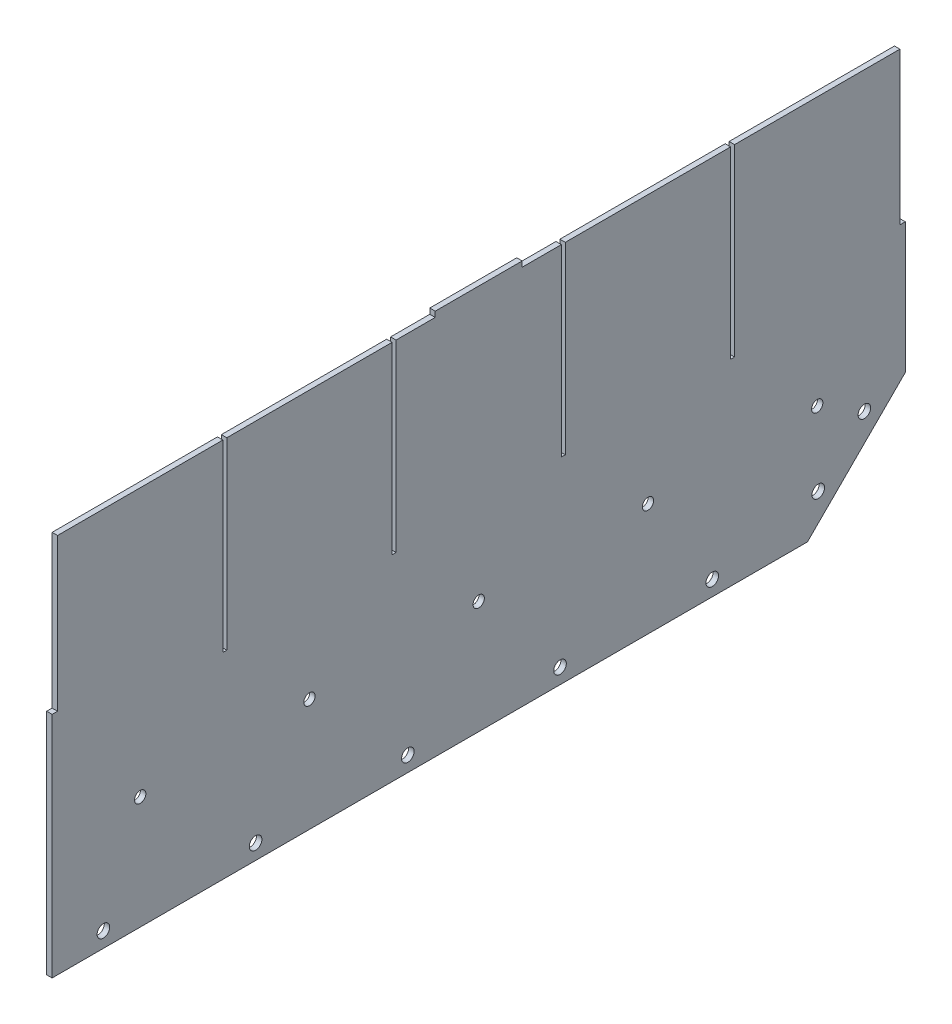
SolidWorks part; units mm, degrees
material "6061-T6 (SS)"
ref_plane "X-Y Datum" through (0, 0, 0) normal (0, 0, 1) x (1, 0, 0)
ref_plane "X-Z Datum" through (0, 0, 0) normal (0, 1, 0) x (1, 0, 0)
ref_plane "Y-Z Datum" through (0, 0, 0) normal (1, 0, 0) x (0, 0, -1)
sketch "Sketch1" plane through (0, 0, 0) normal (1, 0, 0) x (0, 0, -1)
  line L1 (-249.174, 82.55) -> (249.174, 82.55)
  line L2 (-249.174, 82.55) -> (-249.174, -82.55)
  line L3 (-249.174, -82.55) -> (249.174, -82.55)
  line L4 (249.174, 82.55) -> (249.174, -82.55)
  line L5 (-249.174, 82.55) -> (249.174, -82.55) construction
  line L6 (-249.174, -82.55) -> (249.174, 82.55) construction
  point P0 (0, 0)
  dimension "D1" = 165.1
  dimension "D2" = 498.348
extrude "Boss-Extrude1" add sketch "Sketch1" along normal mid plane 3.175
sketch "Sketch2" plane through (1.5875, 0, 0) normal (1, 0, 0) x (0, 0, -1)
  line L3 (192.024, -139.7) -> (-249.174, -139.7)
  line L5 (-249.174, -82.55) -> (249.174, -82.55) construction
  line L6 (-249.174, -82.55) -> (249.174, -82.55)
  line L7 (-249.174, -82.55) -> (-249.174, -139.7)
  line L12 (192.024, -139.7) -> (249.174, -82.55)
  dimension "D1" = 45
  dimension "D5" = 57.15
extrude "Boss-Extrude2" add sketch "Sketch2" against normal blind 3.175
sketch "Sketch3" plane through (1.5875, 0, 0) normal (1, 0, 0) x (0, 0, -1)
  line L0 (-219.202, -139.7) -> (-219.202, -130.81)
  line L1 (192.024, -139.7) -> (-249.174, -139.7) construction
  line L2 (-219.202, -130.81) -> (-249.174, -130.81)
  line L3 (-249.174, 82.55) -> (-249.174, -139.7) construction
  circle A0 centre (-219.202, -130.81) radius 3.675
  dimension "D1" = 29.972
  dimension "D2" = 8.89
extrude "Cut-Extrude1" cut sketch "Sketch3" against normal blind 3.175 contours L2 A0 L0 | L0 A0 L2
pattern_linear "LPattern1" count 5 spacing 88.9 along (0, 0, -1) of "Cut-Extrude1"
sketch "Sketch4" plane through (1.5875, 0, 0) normal (1, 0, 0) x (0, 0, -1)
  line L0 (192.024, -139.7) -> (183.9418, -131.6178)
  line L1 (183.9418, -131.6178) -> (198.3102, -117.2494)
  circle A0 centre (198.3102, -117.2494) radius 3.675
extrude "Cut-Extrude2" cut sketch "Sketch4" against normal through all
pattern_linear "LPattern2" count 2 spacing 38.1 along (0, 0.7071, -0.7071) of "Cut-Extrude2"
sketch "Sketch5" plane through (-1.5875, 0, 0) normal (-1, 0, 0) x (0, 0, 1)
  line L1 (-249.174, 82.55) -> (-245.999, 82.55)
  line L2 (-249.174, 82.55) -> (-249.174, -6.35)
  line L3 (-249.174, -6.35) -> (-245.999, -6.35)
  line L4 (-245.999, 82.55) -> (-245.999, -6.35)
  line L5 (249.174, 82.55) -> (245.999, 82.55)
  line L6 (249.174, 82.55) -> (249.174, -6.35)
  line L7 (249.174, -6.35) -> (245.999, -6.35)
  line L8 (245.999, 82.55) -> (245.999, -6.35)
  dimension "D1" = 3.175
  dimension "D2" = 88.9
  dimension "D3" = 3.175
  dimension "D4" = 88.9
extrude "Cut-Extrude3" cut sketch "Sketch5" against normal through all
sketch "Sketch6" plane through (-1.5875, 0, 0) normal (-1, 0, 0) x (0, 0, 1)
  line L0 (-122.174, 82.55) -> (-249.174, 82.55) construction
  line L1 (-149.4282, 82.55) -> (-149.4282, -24.892) construction
  line L2 (-122.174, 82.55) -> (-249.174, 82.55)
  line L3 (-149.4282, 82.55) -> (-149.4282, -24.892)
  line L5 (-149.4282, 82.55) -> (-147.1422, 82.55)
  line L6 (-149.4282, 82.55) -> (-149.4282, -24.892)
  line L7 (-149.4282, -24.892) -> (-147.1422, -24.892)
  line L8 (-147.1422, 82.55) -> (-147.1422, -24.892)
  dimension "D1" = 2.286
  dimension "D2" = 107.442
extrude "Cut-Extrude4" cut sketch "Sketch6" against normal through all contours L8 L2 L3 L7
pattern_linear "LPattern3" count 4 spacing 98.8568 along (0, 0, 1) of "Cut-Extrude4"
sketch "Sketch7" plane through (-1.5875, 0, 0) normal (-1, 0, 0) x (0, 0, 1)
  line L0 (122.174, 85.725) -> (25.4, 85.725) construction
  line L1 (25.4, 82.55) -> (-25.4, 82.55)
  line L2 (25.4, 82.55) -> (25.4, 85.725)
  line L3 (25.4, 85.725) -> (-25.4, 85.725)
  line L4 (-25.4, 82.55) -> (-25.4, 85.725)
  line L5 (25.4, 82.55) -> (-25.4, 85.725) construction
  line L6 (25.4, 85.725) -> (-25.4, 82.55) construction
  point P0 (0, 84.1375)
  dimension "D1" = 3.175
  dimension "D2" = 50.8
extrude "Boss-Extrude3" add sketch "Sketch7" against normal blind 3.175
sketch "Sketch8" plane through (1.5875, 0, 0) normal (1, 0, 0) x (0, 0, -1)
  line L0 (192.024, -139.7) -> (-249.174, -139.7) construction
  circle A0 centre (0, -73.8124) radius 3
  dimension "D1" = 6
  dimension "D2" = 65.8876
hole_wizard "M6 Clearance Hole1" positions "Sketch9" profile "Sketch10" hole size "M6" standard "ANSI Metric" end condition through all
sketch "Sketch9" plane through (1.5875, 0, 0) normal (1, 0, 0) x (0, 0, -1)
  point P0 (0, -73.8124)
sketch "Sketch10" plane through (1.5875, -73.8124, 0) normal (0, 1, 0) x (0, 0, -1)
  line L0 (0, 0) -> (0, 3.175)
  line L1 (0, 3.175) -> (3.3, 3.175)
  line L2 (3.3, 3.175) -> (3.3, 0)
  line L5 (3.3, 0) -> (0, 0)
  line L11 (0, -6.35) -> (0, 107.95) construction
  dimension "Thru Hole Dia." = 6.6
  dimension "Thru Hole Depth" = 3.175
pattern_linear "LPattern4" count 3 spacing 98.8568 along (0, 0, 1) count 3 spacing 98.8568 along (0, 0, -1) of "M6 Clearance Hole1"
